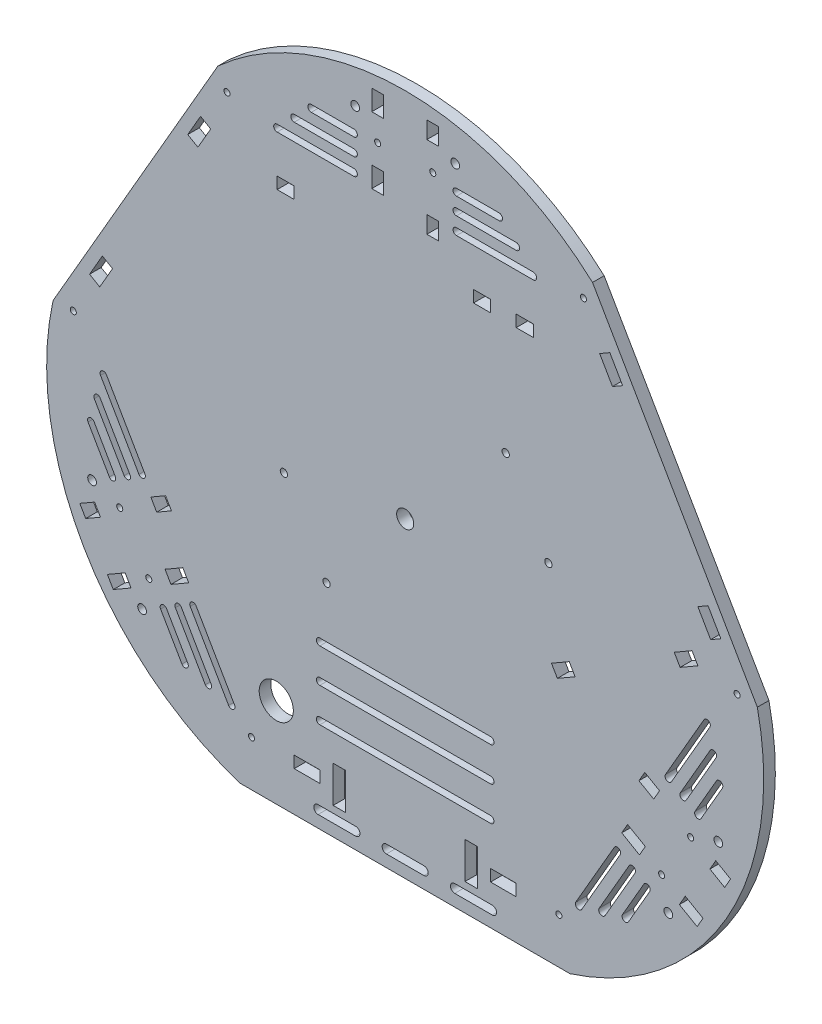
SolidWorks part; units mm, degrees
ref_plane "Front Plane" through (0, 0, 0) normal (0, 0, 1) x (1, 0, 0)
ref_plane "Top Plane" through (0, 0, 0) normal (0, 1, 0) x (1, 0, 0)
ref_plane "Right Plane" through (0, 0, 0) normal (1, 0, 0) x (0, 0, -1)
sketch "Sketch1" plane through (0, 0, 0) normal (0, 0, 1) x (1, 0, 0)
  line L0 (-96.5063, -182.3938) -> (96.5063, -182.3938)
  line L1 (206.2108, 7.62) -> (109.7045, 174.7738)
  line L2 (-109.7045, 174.7738) -> (-206.2108, 7.62)
  line L6 (0, 0) -> (-157.9577, 91.1969) construction
  line L7 (0, 0) -> (157.9577, 91.1969) construction
  line L8 (0, 0) -> (0, -182.3938) construction
  arc A0 (-206.2108, 7.62) -> (-96.5063, -182.3938) centre (-46.9534, -27.1085) ccw
  arc A1 (96.5063, -182.3938) -> (206.2108, 7.62) centre (46.9534, -27.1085) ccw
  arc A2 (109.7045, 174.7738) -> (-109.7045, 174.7738) centre (0, 54.2171) ccw
  circle A3 centre (0, 0) radius 5
  dimension "D1" = 163
  dimension "D6" = 10
  dimension "D2" = 193.0125
  dimension "D3" = 60
  dimension "D4" = 182.3938
  dimension "D5" = 120
extrude "Boss-Extrude1" add sketch "Sketch1" along normal blind 6.8
sketch "Sketch2" plane through (0, 0, 6.8) normal (0, 0, 1) x (1, 0, 0)
  line L0 (0, 0) -> (-157.9577, 91.1969) construction
  line L1 (-109.7045, 174.7738) -> (-206.2108, 7.62) construction
  line L2 (-119.8285, 144.2386) -> (-127.3285, 131.2482)
  line L3 (-127.3285, 131.2482) -> (-121.3702, 127.8082)
  line L4 (-121.3702, 127.8082) -> (-113.8702, 140.7986)
  line L5 (-113.8702, 140.7986) -> (-119.8285, 144.2386)
  line L6 (-104.3494, 164.1692) -> (-116.8494, 142.5186) construction
  line L9 (-194.3494, 8.2846) -> (-181.8494, 29.9352) construction
  line L10 (-177.3285, 44.6456) -> (-171.3702, 41.2056)
  line L11 (-184.8285, 31.6552) -> (-177.3285, 44.6456)
  line L12 (-171.3702, 41.2056) -> (-178.8702, 28.2152)
  line L13 (-178.8702, 28.2152) -> (-184.8285, 31.6552)
  circle A0 centre (-104.3494, 164.1692) radius 1.775
  circle A1 centre (-194.3494, 8.2846) radius 1.775
  dimension "D6" = 3.55
  dimension "D1" = 6.5
  dimension "D2" = 15
  dimension "D3" = 6.88
  dimension "D4" = 50
  dimension "D5" = 25
extrude "Cut-Extrude1" cut sketch "Sketch2" against normal blind 6.8
sketch "Sketch3" plane through (0, 0, 6.8) normal (0, 0, 1) x (1, 0, 0)
  line L0 (0, 0) -> (0, -197.8086) construction
  line L1 (-65, -159.1438) -> (-50, -159.1438)
  line L2 (-65, -159.1438) -> (-65, -152.2638)
  line L3 (-65, -152.2638) -> (-50, -152.2638)
  line L4 (-50, -159.1438) -> (-50, -152.2638)
  line L5 (-65, -159.1438) -> (-50, -152.2638) construction
  line L6 (-65, -152.2638) -> (-50, -159.1438) construction
  line L7 (-96.5063, -182.3938) -> (96.5063, -182.3938) construction
  line L9 (-35, -166.4038) -> (-42.2, -166.4038)
  line L10 (-35, -166.4038) -> (-35, -145.0038)
  line L11 (-35, -145.0038) -> (-42.2, -145.0038)
  line L12 (-42.2, -166.4038) -> (-42.2, -145.0038)
  line L13 (-35, -166.4038) -> (-42.2, -145.0038) construction
  line L14 (-35, -145.0038) -> (-42.2, -166.4038) construction
  circle A0 centre (-90, -155.7038) radius 1.775
  point P0 (-57.5, -155.7038)
  point P12 (-38.6, -155.7038)
  dimension "D5" = 3.55
  dimension "D1" = 50
  dimension "D2" = 6.88
  dimension "D3" = 15
  dimension "D4" = 23.25
  dimension "D6" = 25
  dimension "D7" = 7.2
  dimension "D8" = 21.4
  dimension "D9" = 35
extrude "Cut-Extrude2" cut sketch "Sketch3" against normal blind 6.8
sketch "Sketch4" plane through (0, 0, 6.8) normal (0, 0, 1) x (1, 0, 0)
  line L0 (11, -172.8938) -> (-11, -172.8938) construction
  line L1 (11, -175.3938) -> (-11, -175.3938)
  line L2 (11, -170.3938) -> (-11, -170.3938)
  line L3 (-29, -172.8938) -> (-51, -172.8938) construction
  line L4 (-29, -175.3938) -> (-51, -175.3938)
  line L5 (-29, -170.3938) -> (-51, -170.3938)
  line L6 (-96.5063, -182.3938) -> (96.5063, -182.3938) construction
  arc A0 (11, -175.3938) -> (11, -170.3938) centre (11, -172.8938) ccw
  arc A1 (-11, -170.3938) -> (-11, -175.3938) centre (-11, -172.8938) ccw
  arc A2 (-29, -175.3938) -> (-29, -170.3938) centre (-29, -172.8938) ccw
  arc A3 (-51, -170.3938) -> (-51, -175.3938) centre (-51, -172.8938) ccw
  point P2 (0, -172.8938)
  point P7 (-40, -172.8938)
  dimension "D3" = 2.5
  dimension "D1" = 22
  dimension "D2" = 18
  dimension "D4" = 9.5
extrude "Cut-Extrude3" cut sketch "Sketch4" against normal blind 6.8
sketch "Sketch5" plane through (0, 0, 6.8) normal (0, 0, 1) x (1, 0, 0)
  line L0 (50, -107.3938) -> (-50, -107.3938) construction
  line L1 (50, -109.3938) -> (-50, -109.3938)
  line L2 (50, -105.3938) -> (-50, -105.3938)
  line L3 (-96.5063, -182.3938) -> (96.5063, -182.3938) construction
  arc A0 (50, -109.3938) -> (50, -105.3938) centre (50, -107.3938) ccw
  arc A1 (-50, -105.3938) -> (-50, -109.3938) centre (-50, -107.3938) ccw
  point P2 (0, -107.3938)
  dimension "D2" = 2
  dimension "D1" = 100
  dimension "D3" = 75
extrude "Cut-Extrude4" cut sketch "Sketch5" against normal blind 6.8
mirror "Mirror1" about plane through (0, 0, 0) normal (1, 0, 0) of "Cut-Extrude3", "Cut-Extrude1", "Cut-Extrude2"
sketch "Sketch6" plane through (0, 0, 6.8) normal (0, 0, 1) x (1, 0, 0)
  line L0 (0, 0) -> (-188.1155, -108.6085) construction
  line L1 (-187.0895, -93.3515) -> (-178.4292, -88.3515)
  line L2 (-178.4292, -88.3515) -> (-181.8692, -82.3932)
  line L3 (-181.8692, -82.3932) -> (-190.5295, -87.3932)
  line L4 (-190.5295, -87.3932) -> (-187.0895, -93.3515)
  line L5 (-174.3895, -115.3485) -> (-170.9495, -121.3068)
  line L6 (-170.9495, -121.3068) -> (-160.5572, -115.3068)
  line L7 (-160.5572, -115.3068) -> (-163.9972, -109.3485)
  line L8 (-163.9972, -109.3485) -> (-174.3895, -115.3485)
  line L9 (-148.9603, -63.3932) -> (-140.3, -58.3932)
  line L10 (-140.3, -58.3932) -> (-136.86, -64.3515)
  line L11 (-136.86, -64.3515) -> (-145.5203, -69.3515)
  line L12 (-145.5203, -69.3515) -> (-148.9603, -63.3932)
  line L13 (-140.6145, -95.8485) -> (-130.2222, -89.8485)
  line L14 (-130.2222, -89.8485) -> (-126.7822, -95.8068)
  line L15 (-126.7822, -95.8068) -> (-137.1745, -101.8068)
  line L16 (-137.1745, -101.8068) -> (-140.6145, -95.8485)
  line L17 (-150.1528, -105.3277) -> (-162.2772, -112.3277) construction
  line L18 (-167.1589, -77.8723) -> (-180.1492, -85.3723) construction
  arc A0 (-206.2108, 7.62) -> (-96.5063, -182.3938) centre (-46.9534, -27.1085) ccw construction
  circle A1 centre (-150.1528, -105.3277) radius 1.775
  circle A2 centre (-167.1589, -77.8723) radius 1.775
  circle A3 centre (-173.2051, -100) radius 12.7 construction
  dimension "D10" = 3.55
  dimension "D13" = 25.4
  dimension "D1" = 10
  dimension "D2" = 12
  dimension "D3" = 12.7
  dimension "D4" = 12.7
  dimension "D5" = 38
  dimension "D6" = 27
  dimension "D7" = 6.88
  dimension "D8" = 208.7
  dimension "D9" = 14
  dimension "D11" = 15
  dimension "D12" = 200
extrude "Cut-Extrude5" cut sketch "Sketch6" against normal blind 6.8
mirror "Mirror2" about plane through (0, 0, 0) normal (1, 0, 0) of "Cut-Extrude5"
pattern_circular "CirPattern1" count 3 over 360 about axis through (0, 0, 6.8) along (0, 0, 1) skipping 1 of "Cut-Extrude5"
sketch "Sketch7" plane through (0, 0, 6.8) normal (0, 0, 1) x (1, 0, 0)
  line L0 (0, 0) -> (-188.1155, -108.6085) construction
  line L1 (0, 0) -> (-154.0667, -122.7699) construction
  line L2 (0, 0) -> (-183.3552, -72.0408) construction
  circle A0 centre (-154.0667, -122.7699) radius 2.55
  circle A1 centre (-183.3552, -72.0408) radius 2.55
  circle A2 centre (0, 0) radius 197 construction
  arc A3 (-206.2108, 7.62) -> (-96.5063, -182.3938) centre (-46.9534, -27.1085) ccw construction
  dimension "D1" = 5.1
  dimension "D2" = 394
  dimension "D3" = 8.55
  dimension "D4" = 8.55
extrude "Cut-Extrude6" cut sketch "Sketch7" against normal blind 6.8
pattern_circular "CirPattern2" count 3 over 360 about axis through (0, 0, 0) along (0, 0, 1) of "Cut-Extrude6"
sketch "Sketch8" plane through (0, 0, 6.8) normal (0, 0, 1) x (1, 0, 0)
  line L1 (75, 129.5) -> (65, 129.5)
  line L2 (75, 129.5) -> (75, 136.38)
  line L3 (75, 136.38) -> (65, 136.38)
  line L4 (65, 129.5) -> (65, 136.38)
  line L5 (75, 129.5) -> (65, 136.38) construction
  line L6 (75, 136.38) -> (65, 129.5) construction
  line L7 (50, 129.5) -> (40, 129.5)
  line L8 (50, 129.5) -> (50, 136.38)
  line L9 (50, 136.38) -> (40, 136.38)
  line L10 (40, 129.5) -> (40, 136.38)
  line L11 (50, 129.5) -> (40, 136.38) construction
  line L12 (50, 136.38) -> (40, 129.5) construction
  line L13 (-65, 129.5) -> (-75, 129.5)
  line L14 (-65, 129.5) -> (-65, 136.38)
  line L15 (-65, 136.38) -> (-75, 136.38)
  line L16 (-75, 129.5) -> (-75, 136.38)
  line L17 (-65, 129.5) -> (-75, 136.38) construction
  line L18 (-65, 136.38) -> (-75, 129.5) construction
  circle A0 centre (0, 0) radius 5 construction
  point P0 (70, 132.94)
  point P5 (45, 132.94)
  point P10 (-70, 132.94)
  dimension "D1" = 10
  dimension "D2" = 6.88
  dimension "D3" = 105
  dimension "D4" = 15
  dimension "D5" = 129.5
  dimension "D6" = 75
extrude "Cut-Extrude7" cut sketch "Sketch8" against normal blind 6.8
sketch "Sketch9" plane through (0, 0, 6.8) normal (0, 0, 1) x (1, 0, 0)
  line L0 (-104.7357, 145.38) -> (-26.88, 145.38)
  line L1 (-26.88, 145.38) -> (-26.88, 176.8458)
  line L2 (-26.88, 176.8458) -> (-42.7928, 192.7587)
  line L3 (-104.7357, 145.38) -> (-93.2711, 165.2374)
  line L4 (-65, 136.38) -> (-75, 136.38) construction
  line L5 (-19.58, 169.7) -> (-19.58, 157.7) construction
  line L6 (-109.7045, 174.7738) -> (-206.2108, 7.62) construction
  line L8 (6, 152) -> (-6, 152) construction
  line L9 (6, 152) -> (6, 207) construction
  line L10 (6, 207) -> (-6, 207) construction
  line L11 (-6, 152) -> (-6, 207) construction
  line L12 (6, 152) -> (-6, 207) construction
  line L13 (6, 207) -> (-6, 152) construction
  circle A1 centre (-29.2885, 194.8106) radius 2.55 construction
  arc A2 (97.5899, 161.4608) -> (-97.5899, 161.4608) centre (0, 54.2171) ccw
  arc A3 (-42.7928, 192.7587) -> (-93.2711, 165.2374) centre (0, 54.2171) ccw
  point P16 (0, 179.5)
  dimension "D5" = 11
  dimension "D2" = 9
  dimension "D3" = 135
  dimension "D4" = 7.3
  dimension "D6" = 19
  dimension "D7" = 12
  dimension "D8" = 55
  dimension "D9" = 152
  dimension "D1" = 18
extrude "Cut-Extrude8" [suppressed] cut sketch "Sketch9" against normal blind 6.8
fillet "Fillet1" [suppressed] radius 5
mirror "Mirror3" [suppressed] about plane through (0, 0, 0) normal (1, 0, 0)
sketch "Sketch10" plane through (0, 0, 6.8) normal (0, 0, 1) x (1, 0, 0)
  line L1 (0, 0) -> (0, -229.3776) construction
  circle A0 centre (-75.5, -130) radius 10
  circle A3 centre (-156, -41) radius 10 construction
  circle A4 centre (0, 0) radius 5 construction
  circle A5 centre (156, -41) radius 10 construction
  dimension "D3" = 20
  dimension "D1" = 130
  dimension "D2" = 75.5
  dimension "D4" = 156
  dimension "D5" = 41
extrude "Cut-Extrude9" cut sketch "Sketch10" against normal blind 6.8
sketch "Sketch11" plane through (0, 0, 0) normal (0, 0, -1) x (-1, 0, 0)
  line L0 (-71.3551, 41.1969) -> (-157.9577, 91.1969) construction
  line L1 (71.0487, -12.1525) -> (-58.8551, 62.8475) construction
  line L2 (71.0487, -12.1525) -> (46.0487, -55.4537) construction
  line L3 (206.2108, 7.62) -> (109.7045, 174.7738)
  line L4 (-109.7045, 174.7738) -> (-206.2108, 7.62)
  line L5 (-96.5063, -182.3938) -> (96.5063, -182.3938)
  line L6 (206.2108, 7.62) -> (109.7045, 174.7738)
  line L7 (-109.7045, 174.7738) -> (-206.2108, 7.62)
  line L8 (-96.5063, -182.3938) -> (96.5063, -182.3938)
  line L9 (46.0487, -55.4537) -> (-83.8551, 19.5463) construction
  line L10 (-58.8551, 62.8475) -> (-83.8551, 19.5463) construction
  circle A4 centre (-83.8551, 19.5463) radius 2.125
  circle A5 centre (-58.8551, 62.8475) radius 2.125
  circle A6 centre (71.0487, -12.1525) radius 2.125
  circle A7 centre (46.0487, -55.4537) radius 2.125
  arc A11 (96.5063, -182.3938) -> (206.2108, 7.62) centre (46.9534, -27.1085) ccw
  arc A12 (109.7045, 174.7738) -> (-109.7045, 174.7738) centre (0, 54.2171) ccw
  arc A13 (-206.2108, 7.62) -> (-96.5063, -182.3938) centre (-46.9534, -27.1085) ccw
  arc A14 (96.5063, -182.3938) -> (206.2108, 7.62) centre (46.9534, -27.1085) ccw
  arc A15 (109.7045, 174.7738) -> (-109.7045, 174.7738) centre (0, 54.2171) ccw
  arc A16 (-206.2108, 7.62) -> (-96.5063, -182.3938) centre (-46.9534, -27.1085) ccw
  dimension "D6" = 4.25
  dimension "D2" = 50
  dimension "D3" = 150
  dimension "D4" = 100
  dimension "D1" = 0
extrude "Cut-Extrude10" cut sketch "Sketch11" against normal blind 10 contours A6 | A7 | A4 | A5
pattern_circular "CirPattern3" [suppressed] count 3 over 360
sketch "Sketch12" plane through (0, 0, 6.8) normal (0, 0, 1) x (1, 0, 0)
  line L0 (30, 160.7) -> (75, 160.7) construction
  line L1 (30, 162.7) -> (75, 162.7)
  line L2 (30, 158.7) -> (75, 158.7)
  line L3 (65, 170.7) -> (30, 170.7) construction
  line L4 (65, 168.7) -> (30, 168.7)
  line L5 (65, 172.7) -> (30, 172.7)
  line L6 (55, 180.7) -> (30, 180.7) construction
  line L7 (55, 178.7) -> (30, 178.7)
  line L8 (55, 182.7) -> (30, 182.7)
  line L9 (19.58, 160.7) -> (12.7, 160.7) construction
  line L10 (0, 0) -> (0, 301.9764) construction
  line L11 (-30, 160.7) -> (-75, 160.7) construction
  line L12 (-30, 162.7) -> (-75, 162.7)
  line L13 (-30, 158.7) -> (-75, 158.7)
  line L14 (-65, 170.7) -> (-30, 170.7) construction
  line L15 (-65, 168.7) -> (-30, 168.7)
  line L16 (-65, 172.7) -> (-30, 172.7)
  line L17 (-55, 180.7) -> (-30, 180.7) construction
  line L18 (-55, 178.7) -> (-30, 178.7)
  line L19 (-55, 182.7) -> (-30, 182.7)
  arc A0 (30, 162.7) -> (30, 158.7) centre (30, 160.7) ccw
  arc A1 (75, 158.7) -> (75, 162.7) centre (75, 160.7) ccw
  arc A2 (65, 168.7) -> (65, 172.7) centre (65, 170.7) ccw
  arc A3 (30, 172.7) -> (30, 168.7) centre (30, 170.7) ccw
  arc A4 (55, 178.7) -> (55, 182.7) centre (55, 180.7) ccw
  arc A5 (30, 182.7) -> (30, 178.7) centre (30, 180.7) ccw
  arc A6 (-30, 162.7) -> (-30, 158.7) centre (-30, 160.7) cw
  arc A7 (-75, 158.7) -> (-75, 162.7) centre (-75, 160.7) cw
  arc A8 (-65, 168.7) -> (-65, 172.7) centre (-65, 170.7) cw
  arc A9 (-30, 172.7) -> (-30, 168.7) centre (-30, 170.7) cw
  arc A10 (-55, 178.7) -> (-55, 182.7) centre (-55, 180.7) cw
  arc A11 (-30, 182.7) -> (-30, 178.7) centre (-30, 180.7) cw
  point P2 (52.5, 160.7)
  point P9 (47.5, 170.7)
  point P16 (42.5, 180.7)
  point P28 (-52.5, 160.7)
  point P35 (-47.5, 170.7)
  point P42 (-42.5, 180.7)
  dimension "D1" = 2
  dimension "D2" = 2
  dimension "D3" = 2
  dimension "D4" = 10
  dimension "D5" = 10
  dimension "D6" = 45
  dimension "D7" = 35
  dimension "D8" = 25
  dimension "D9" = 30
extrude "Cut-Extrude11" cut sketch "Sketch12" against normal through all
pattern_circular "CirPattern4" count 3 over 360 about axis through (0, 0, 0) along (0, 0, 1) of "Cut-Extrude11"
pattern_linear "LPattern1" count 2 spacing 20 along (0, 1, 0) count 2 spacing 20 along (0, -1, 0) of "Cut-Extrude4"
sketch "Sketch14" plane through (0, 0, 0) normal (0, 0, -1) x (-1, 0, 0)
  line L4 (-171.3799, 11.189) -> (-167.9399, 17.1472)
  line L5 (-157.5476, 11.1472) -> (-160.9876, 5.189)
  line L6 (-85.6674, -30.3528) -> (-89.1074, -36.311)
  line L7 (-99.4998, -30.311) -> (-96.0598, -24.3528)
  line L8 (-167.9399, 17.1472) -> (-157.5476, 11.1472)
  line L9 (-160.9876, 5.189) -> (-171.3799, 11.189)
  line L10 (-96.0598, -24.3528) -> (-85.6674, -30.3528)
  line L11 (-89.1074, -36.311) -> (-99.4998, -30.311)
  line L12 (-184.8285, 31.6552) -> (-178.8702, 28.2152) construction
  line L13 (-206.2108, 7.62) -> (-109.7045, 174.7738) construction
  point P8 (-181.8494, 29.9352)
  dimension "D1" = 4.12
  dimension "D2" = 28.38
  dimension "D3" = 71
  dimension "D4" = 12
  dimension "D5" = 6.88
extrude "Cut-Extrude12" cut sketch "Sketch14" against normal through all
